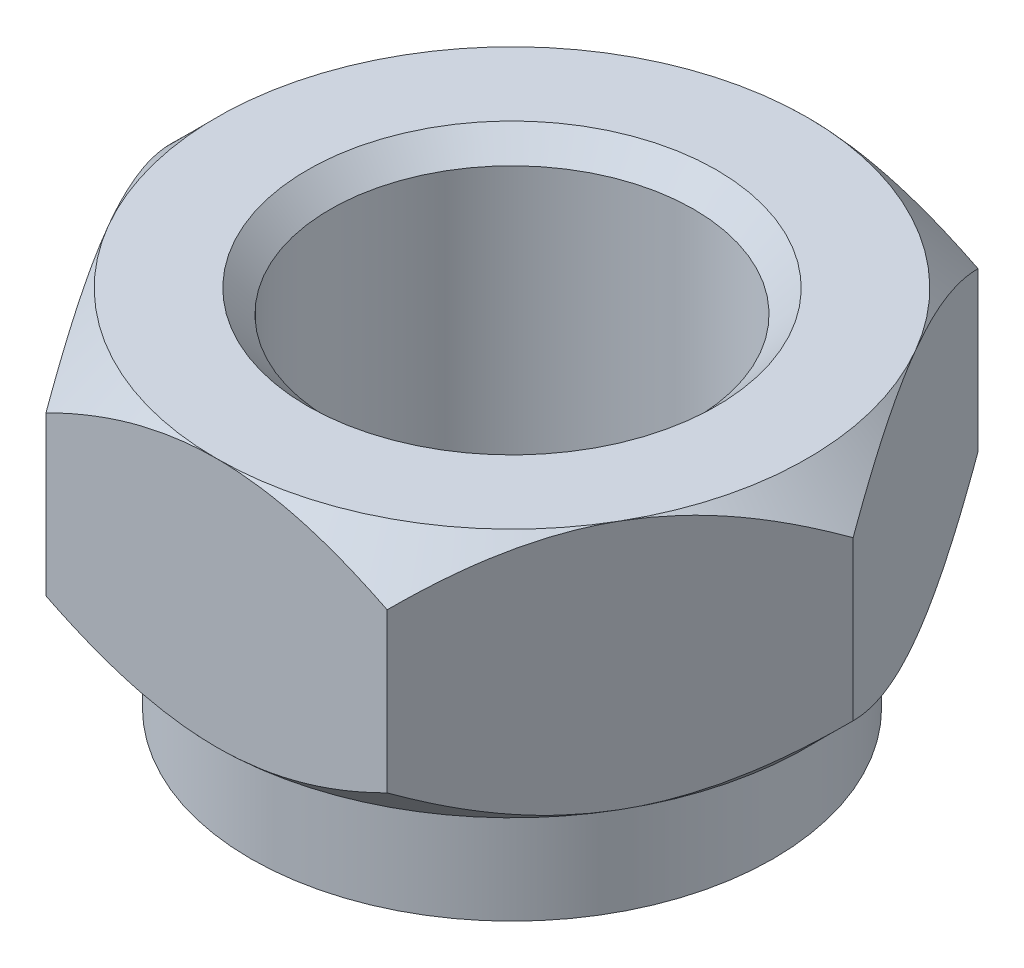
SolidWorks part; units mm, degrees
ref_plane "Płaszczyzna przednia" through (0, 0, 0) normal (0, 0, 1) x (1, 0, 0)
ref_plane "Płaszczyzna górna" through (0, 0, 0) normal (0, 1, 0) x (1, 0, 0)
ref_plane "Płaszczyzna prawa" through (0, 0, 0) normal (1, 0, 0) x (0, 0, -1)
sketch "Szkic1" plane through (0, 0, 0) normal (0, 1, 0) x (1, 0, 0)
  line L1 (7.5056, 0) -> (3.7528, 6.5)
  line L2 (3.7528, 6.5) -> (-3.7528, 6.5)
  line L3 (-3.7528, 6.5) -> (-7.5056, 0)
  line L4 (-7.5056, 0) -> (-3.7528, -6.5)
  line L5 (-3.7528, -6.5) -> (3.7528, -6.5)
  line L6 (3.7528, -6.5) -> (7.5056, 0)
  circle A0 centre (0, 0) radius 6.5 construction
  circle A1 centre (0, 0) radius 4
  dimension "D2" = 8
  dimension "D1" = 13
extrude "Dodanie-wyciągnięcie1" add sketch "Szkic1" along normal blind 5.5
sketch "Szkic2" plane through (0, 5.5, 0) normal (0, 1, 0) x (1, 0, 0)
  line L3 (3.7528, -6.5) -> (7.5056, 0) construction
  line L4 (3.7528, 6.5) -> (-3.7528, 6.5) construction
  line L5 (-7.5056, 0) -> (-3.7528, -6.5) construction
  circle A0 centre (0, 0) radius 6.5
extrude "Wytnij-wyciągnięcie29" cut sketch "Szkic2" against normal through all draft 45 flip side to cut contours A0
sketch "Szkic4" plane through (0, 0, 0) normal (0, -1, 0) x (-1, 0, 0)
  circle A0 centre (0, 0) radius 5.75
  circle A1 centre (0, 0) radius 4
  circle A2 centre (0, 0) radius 4 construction
  dimension "D1" = 11.5
extrude "Dodanie-wyciągnięcie2" add sketch "Szkic4" along normal blind 2.5
sketch "Szkic5" plane through (0, 0, 0) normal (0, -1, 0) x (-1, 0, 0)
  line L0 (3.7528, -6.5) -> (-3.7528, -6.5) construction
  circle A0 centre (0, 0) radius 6.5
extrude "Wytnij-wyciągnięcie30" cut sketch "Szkic5" against normal blind 10 draft 45 flip side to cut
fillet "Zaokrąglenie1" radius 0.1 1 edges at (0, 0, -5.75)
chamfer "Sfazowanie1" distance 0.5 angle 45 2 edges at (0, -2.5, -4) (0, 5.5, 4)
